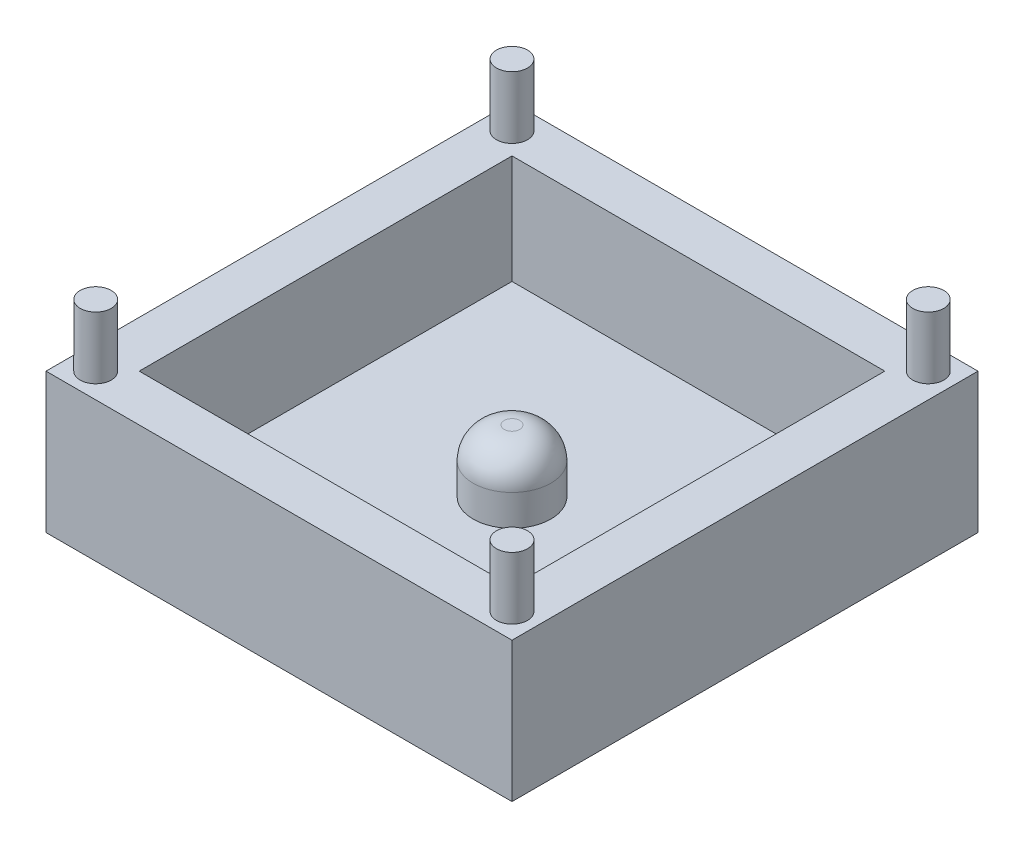
SolidWorks part; units mm, degrees
ref_plane "Front Plane" through (0, 0, 0) normal (0, 0, 1) x (1, 0, 0)
ref_plane "Top Plane" through (0, 0, 0) normal (0, 1, 0) x (1, 0, 0)
ref_plane "Right Plane" through (0, 0, 0) normal (1, 0, 0) x (0, 0, -1)
sketch "Sketch1" plane through (0, 0, 0) normal (0, 1, 0) x (1, 0, 0)
  line L1 (-7.5, -7.5) -> (7.5, -7.5)
  line L2 (-7.5, -7.5) -> (-7.5, 7.5)
  line L3 (-7.5, 7.5) -> (7.5, 7.5)
  line L4 (7.5, -7.5) -> (7.5, 7.5)
  line L5 (-7.5, -7.5) -> (7.5, 7.5) construction
  line L6 (-7.5, 7.5) -> (7.5, -7.5) construction
  point P0 (0, 0)
  dimension "D1" = 15
  dimension "D2" = 15
extrude "Boss-Extrude1" add sketch "Sketch1" along normal blind 4.5
sketch "Sketch2" plane through (0, 4.5, 0) normal (0, 1, 0) x (1, 0, 0)
  line L1 (-6, -6) -> (6, -6)
  line L2 (-6, -6) -> (-6, 6)
  line L3 (-6, 6) -> (6, 6)
  line L4 (6, -6) -> (6, 6)
  line L5 (-6, -6) -> (6, 6) construction
  line L6 (-6, 6) -> (6, -6) construction
  point P0 (0, 0)
  dimension "D1" = 12
  dimension "D2" = 12
extrude "Cut-Extrude1" cut sketch "Sketch2" against normal blind 3.5
sketch "Sketch3" plane through (0, 1, 0) normal (0, 1, 0) x (1, 0, 0)
  circle A0 centre (0, 0) radius 1.25
  dimension "D1" = 2.5
extrude "Boss-Extrude2" add sketch "Sketch3" along normal blind 2
fillet "Fillet1" radius 1 1 edges at (0, 3, 1.25)
sketch "Sketch4" plane through (0, 4.5, 0) normal (0, 1, 0) x (1, 0, 0)
  line L0 (-7.5, -7.5) -> (7.5, -7.5) construction
  line L1 (-7.5, 7.5) -> (-7.5, -7.5) construction
  line L2 (7.5, -7.5) -> (7.5, 7.5) construction
  line L3 (7.5, 7.5) -> (-7.5, 7.5) construction
  circle A0 centre (-6.7, 6.7) radius 0.5
  circle A1 centre (6.7, 6.7) radius 0.5
  circle A2 centre (6.7, -6.7) radius 0.5
  circle A3 centre (-6.7, -6.7) radius 0.5
  dimension "D1" = 1
  dimension "D2" = 1
  dimension "D3" = 1
  dimension "D4" = 1
  dimension "D5" = 0.8
  dimension "D6" = 0.8
  dimension "D7" = 0.8
  dimension "D8" = 0.8
  dimension "D9" = 0.8
  dimension "D10" = 0.8
  dimension "D11" = 0.8
  dimension "D12" = 0.8
extrude "Boss-Extrude3" add sketch "Sketch4" along normal blind 2
